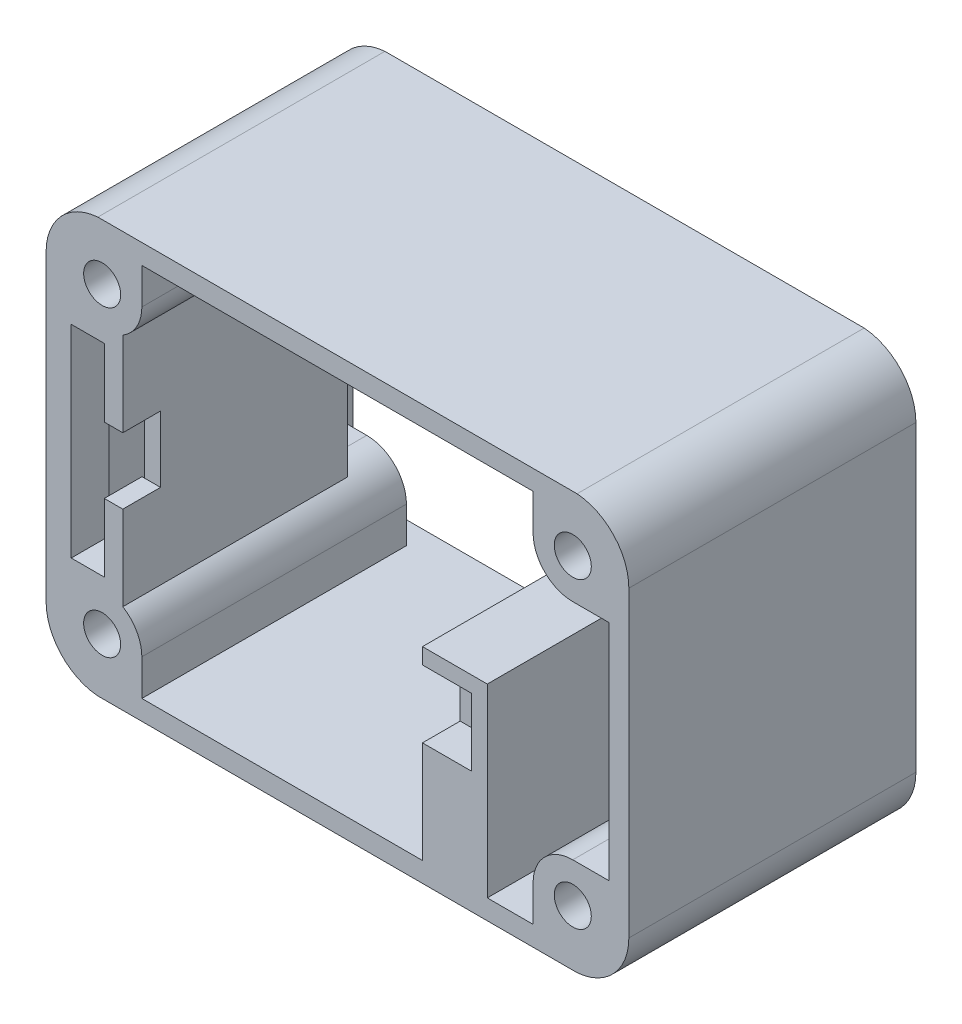
SolidWorks part; units mm, degrees
ref_plane "Front Plane" through (0, 0, 0) normal (0, 0, 1) x (1, 0, 0)
ref_plane "Top Plane" through (0, 0, 0) normal (0, 1, 0) x (1, 0, 0)
ref_plane "Right Plane" through (0, 0, 0) normal (1, 0, 0) x (0, 0, -1)
sketch "Sketch1" plane through (0, 0, 0) normal (0, 0, 1) x (1, 0, 0)
  line L0 (-20.325, 13.975) -> (-20.325, 14.175) construction
  line L1 (-22.025, -15.675) -> (22.025, -15.675)
  line L2 (-22.025, -15.675) -> (-22.025, 15.675)
  line L3 (-22.025, 15.675) -> (22.025, 15.675)
  line L4 (20.325, -13.975) -> (20.325, 13.975)
  line L5 (20.325, 13.975) -> (-20.325, 13.975)
  line L6 (-20.325, 13.975) -> (-20.325, -13.975)
  line L7 (-20.325, -13.975) -> (20.325, -13.975)
  line L8 (20.325, -13.975) -> (20.325, 13.975)
  line L9 (20.325, 13.975) -> (-20.325, 13.975)
  line L10 (-20.325, 13.975) -> (-20.325, -13.975)
  line L11 (-20.325, -13.975) -> (20.325, -13.975)
  line L12 (22.025, -15.675) -> (22.025, 15.675)
  line L13 (-22.025, -15.675) -> (22.025, 15.675) construction
  line L14 (-22.025, 15.675) -> (22.025, -15.675) construction
  line L15 (-20.325, 13.975) -> (-20.525, 13.975) construction
  line L16 (-14.7875, 11.45) -> (-14.7875, 14.175)
  line L17 (-17.7875, 8.45) -> (-20.525, 8.45)
  line L18 (0, 15.675) -> (0, -15.675) construction
  line L19 (-22.025, 0) -> (22.025, 0) construction
  line L20 (14.7875, 11.45) -> (14.7875, 14.175)
  line L21 (17.7875, 8.45) -> (20.525, 8.45)
  line L22 (17.7875, -8.45) -> (20.525, -8.45)
  line L23 (14.7875, -11.45) -> (14.7875, -14.175)
  line L24 (-14.7875, -11.45) -> (-14.7875, -14.175)
  line L25 (-17.7875, -8.45) -> (-20.525, -8.45)
  line L26 (-20.525, 14.175) -> (-22.025, 14.175) construction
  line L27 (20.525, -14.175) -> (-20.525, -14.175)
  line L28 (20.525, -14.175) -> (20.525, 14.175)
  line L29 (20.525, 14.175) -> (-20.525, 14.175)
  line L30 (-20.525, -14.175) -> (-20.525, 14.175)
  line L31 (20.525, -14.175) -> (-20.525, 14.175) construction
  line L32 (20.525, 14.175) -> (-20.525, -14.175) construction
  line L33 (-20.525, 14.175) -> (-20.525, 15.675) construction
  circle A0 centre (-17.7875, 11.45) radius 1.4
  circle A1 centre (17.7875, 11.45) radius 3
  circle A2 centre (17.7875, -11.45) radius 3
  circle A3 centre (-17.7875, -11.45) radius 3
  circle A4 centre (-17.7875, 11.45) radius 3
  circle A5 centre (17.7875, 11.45) radius 1.4
  circle A6 centre (17.7875, -11.45) radius 1.4
  circle A7 centre (-17.7875, -11.45) radius 1.4
  point P9 (0, 0)
  point P16 (0, 0)
  point P44 (-19.0562, -8.45)
  dimension "D2" = 2.8
  dimension "D4" = 6
  dimension "D3" = 1.5
  dimension "D5" = 0.2
  dimension "D1" = 0
extrude "Boss-Extrude1" add sketch "Sketch1" along normal blind 20 contours A4 L16 L9 | A4 L9 L16 L29 | L1 L12 L3 L2 A4 L29 A1 L28 A2 L27 A3 L30 | L29 A4 | A4 L29 L30 L10 L9 | A4 L9 L10 | L9 A4 L29 | L30 A4 | L10 A4 L30 | L9 A4 L10 A0 | A4 L30 L17 L10 | A4 L10 L17 | A1 L29 | L29 A1 L9 L8 L28 | L9 A1 L8 | A1 L8 L9 A5 | A1 L9 L29 | A1 L28 L8 | A1 L28 | L8 A1 L21 | L28 A1 L8 L21 | L20 A1 L9 | L9 A1 L29 L20 | A2 L28 L22 L8 | A2 L8 L22 | L8 A2 L11 A6 | L28 A2 | L28 A2 L8 | A2 L27 L28 L8 L11 | A2 L11 L8 | L11 A2 L27 | L27 A2 | A2 L23 L11 | A2 L11 L23 L27 | L27 A3 L11 L10 L30 | L11 A3 L10 | A3 L10 L30 | A3 L30 | L30 A3 L10 L25 | L10 A3 L25 | A3 L11 L10 A7 | A3 L11 L27 | A3 L27 | L24 A3 L11 | L11 A3 L27 L24
sketch "Sketch2" plane through (0, 0, 0) normal (0, 0, -1) x (-1, 0, 0)
  line L0 (-14.7875, 14.175) -> (14.7875, 14.175) construction
  line L2 (-20.525, 14.175) -> (20.525, 14.175)
  line L3 (-20.525, 14.175) -> (-20.525, -14.175)
  line L4 (-20.525, -14.175) -> (20.525, -14.175)
  line L5 (-22.025, -15.675) -> (22.025, -15.675)
  line L6 (22.025, -15.675) -> (22.025, 15.675)
  line L7 (22.025, 15.675) -> (-22.025, 15.675)
  line L8 (-22.025, 15.675) -> (-22.025, -15.675)
  line L9 (-22.025, -15.675) -> (22.025, -15.675)
  line L10 (22.025, -15.675) -> (22.025, 15.675)
  line L11 (22.025, 15.675) -> (-22.025, 15.675)
  line L12 (-22.025, 15.675) -> (-22.025, -15.675)
  line L13 (20.525, 14.175) -> (20.525, -14.175)
  line L14 (-20.525, -8.45) -> (-20.525, 8.45) construction
  line L15 (20.525, -8.45) -> (20.525, 8.45) construction
  line L16 (-14.7875, -14.175) -> (14.7875, -14.175) construction
  line L17 (0, 14.175) -> (0, -14.175) construction
  line L18 (-20.525, 0) -> (20.525, 0) construction
  line L19 (2, -14.925) -> (2, -14.175)
  line L20 (-2, 14.925) -> (2, 14.925)
  line L21 (-2, 14.925) -> (-2, 14.175)
  line L22 (-2, 14.175) -> (2, 14.175)
  line L23 (2, 14.925) -> (2, 14.175)
  line L24 (-2, 14.925) -> (2, 14.175) construction
  line L25 (-2, 14.175) -> (2, 14.925) construction
  line L26 (-21.275, -2) -> (-20.525, -2)
  line L27 (-21.275, -2) -> (-21.275, 2)
  line L28 (-21.275, 2) -> (-20.525, 2)
  line L29 (-20.525, -2) -> (-20.525, 2)
  line L30 (-21.275, -2) -> (-20.525, 2) construction
  line L31 (-21.275, 2) -> (-20.525, -2) construction
  line L32 (-2, -14.925) -> (2, -14.925)
  line L33 (-2, -14.925) -> (-2, -14.175)
  line L34 (21.275, 2) -> (20.525, 2)
  line L35 (21.275, -2) -> (21.275, 2)
  line L36 (21.275, -2) -> (20.525, -2)
  point P20 (0, 14.55)
  point P25 (-20.9, 0)
  line M25 (-22.025, -15.675) -> (22.025, -15.675)
  line M26 (22.025, -15.675) -> (22.025, 15.675)
  line M27 (22.025, 15.675) -> (-22.025, 15.675)
  line M28 (-22.025, 15.675) -> (-22.025, -15.675)
  line M36 (20.525, 8.45) -> (20.525, -8.45)
  line M41 (-14.7875, 14.175) -> (14.7875, 14.175)
  line M62 (14.7875, -14.175) -> (-14.7875, -14.175)
  line M63 (-20.525, -8.45) -> (-20.525, 8.45)
  dimension "D2" = 0.75
  dimension "D3" = 4
  dimension "D1" = 0
extrude "Boss-Extrude2" add sketch "Sketch2" along normal blind 1.7 contours L35 L36 L13 L4 L19 L32 L33 L3 L26 L27 L28 L2 L21 L20 L23 L34 M28 M25 M26 M27 M36 M62 M63 M41
ref_plane "Plane1" through (0, 0, 3) normal (0, 0, -1) x (-1, 0, 0)
sketch "Sketch3" plane through (0, 0, 3) normal (0, 0, -1) x (-1, 0, 0)
  line L0 (-20.525, 0) -> (20.525, 0) construction
  line L1 (-20.525, -2) -> (-20.525, 2) construction
  line L2 (20.525, -2) -> (20.525, 2) construction
  line L4 (-20.525, -8.45) -> (-20.525, 8.45) construction
  line L33 (20.525, 14.175) -> (20.525, 2) construction
  line L34 (16.225, -8.45) -> (20.525, -8.45)
  line L35 (16.225, -8.45) -> (16.225, 8.45)
  line L36 (16.225, 8.45) -> (20.525, 8.45)
  line L37 (20.525, -8.45) -> (20.525, 8.45)
  line L38 (16.225, -8.45) -> (20.525, 8.45) construction
  line L39 (16.225, 8.45) -> (20.525, -8.45) construction
  line L40 (17.7875, 8.45) -> (20.525, 8.45) construction
  line L41 (16.225, 8.45) -> (16.225, 8.889)
  line L42 (16.225, -8.45) -> (16.225, -8.889)
  line L43 (-8.875, 14.175) -> (-8.875, -14.175) construction
  line L44 (20.325, -7.85) -> (17.425, -7.85)
  line L45 (20.325, -7.85) -> (20.325, 7.85)
  line L46 (20.325, 7.85) -> (17.425, 7.85)
  line L47 (17.425, -7.85) -> (17.425, 7.85)
  line L48 (20.325, -7.85) -> (17.425, 7.85) construction
  line L49 (20.325, 7.85) -> (17.425, -7.85) construction
  line L50 (-20.525, 14.175) -> (-2, 14.175) construction
  line L51 (-2, -14.175) -> (-20.525, -14.175) construction
  line L52 (-10.325, -1.175) -> (-10.325, -0.175) construction
  line L53 (-6.425, -0.175) -> (-11.325, -0.175)
  line L54 (-6.425, -0.175) -> (-6.425, -14.175)
  line L55 (-6.425, -14.175) -> (-11.325, -14.175)
  line L56 (-11.325, -0.175) -> (-11.325, -14.175)
  line L57 (-6.425, -0.175) -> (-11.325, -14.175) construction
  line L58 (-6.425, -14.175) -> (-11.325, -0.175) construction
  line L59 (-10.325, -1.175) -> (-7.425, -1.175)
  line L60 (-10.325, -1.175) -> (-10.325, -6.675)
  line L61 (-10.325, -6.675) -> (-7.425, -6.675)
  line L62 (-7.425, -1.175) -> (-7.425, -6.675)
  line L63 (-10.325, -1.175) -> (-7.425, -6.675) construction
  line L64 (-10.325, -6.675) -> (-7.425, -1.175) construction
  line L65 (-10.325, -1.175) -> (-11.325, -1.175) construction
  arc A0 (-17.7875, 8.45) -> (-14.7875, 11.45) centre (-17.7875, 11.45) ccw construction
  arc A1 (-14.7875, -11.45) -> (-17.7875, -8.45) centre (-17.7875, -11.45) ccw construction
  arc A2 (-17.7875, 8.45) -> (-14.7875, 11.45) centre (-17.7875, 11.45) ccw
  arc A3 (-14.7875, -11.45) -> (-17.7875, -8.45) centre (-17.7875, -11.45) ccw
  arc A4 (14.7875, 11.45) -> (17.7875, 8.45) centre (17.7875, 11.45) ccw construction
  arc A5 (17.7875, -8.45) -> (14.7875, -11.45) centre (17.7875, -11.45) ccw construction
  arc A6 (17.7875, -8.45) -> (14.7875, -11.45) centre (17.7875, -11.45) ccw
  arc A7 (14.7875, 11.45) -> (17.7875, 8.45) centre (17.7875, 11.45) ccw
  point P41 (18.375, 0)
  point P58 (18.875, 0)
  point P71 (-8.875, -7.175)
  point P76 (-8.875, -3.925)
  dimension "D2" = 0.2
  dimension "D3" = 10.2
  dimension "D4" = 7.5
  dimension "D6" = 4.3
  dimension "D7" = 15.7
  dimension "D8" = 2.9
  dimension "D9" = 1
  dimension "D10" = 5.5
extrude "Boss-Extrude3" add sketch "Sketch3" against normal blind 14.15
sketch "Sketch4" plane through (0, 0, 17.15) normal (0, 0, 1) x (1, 0, 0)
  line L18 (11.325, -0.175) -> (6.425, -0.175)
  line L20 (-20.525, -8.45) -> (-17.7875, -8.45)
  line L21 (-16.225, -8.889) -> (-16.225, 8.889)
  line L22 (-17.7875, 8.45) -> (-20.525, 8.45)
  line L23 (-20.525, 8.45) -> (-20.525, -8.45)
  line L24 (-20.525, -8.45) -> (-17.7875, -8.45)
  line L25 (-16.225, -8.889) -> (-16.225, 8.889)
  line L26 (-17.7875, 8.45) -> (-20.525, 8.45)
  line L27 (-20.525, 8.45) -> (-20.525, -8.45)
  line L33 (-20.125, -7.65) -> (-17.625, -7.65)
  line L34 (-20.125, 7.65) -> (-20.125, -7.65)
  line L35 (11.325, -14.175) -> (11.325, -0.175)
  line L36 (6.425, -14.175) -> (11.325, -14.175)
  line L37 (6.425, -0.175) -> (6.425, -14.175)
  line L38 (11.325, -0.175) -> (6.425, -0.175)
  line L39 (11.325, -14.175) -> (11.325, -0.175)
  line L40 (6.425, -14.175) -> (11.325, -14.175)
  line L41 (6.425, -0.175) -> (6.425, -14.175)
  line L42 (-17.625, 7.65) -> (-20.125, 7.65)
  line L43 (-17.625, -7.65) -> (-17.625, 7.65)
  line L44 (-20.125, -7.65) -> (-17.625, -7.65)
  line L45 (-20.125, 7.65) -> (-20.125, -7.65)
  line L46 (7.625, -6.475) -> (10.125, -6.475)
  line L47 (7.625, -1.375) -> (7.625, -6.475)
  line L48 (10.125, -6.475) -> (10.125, -1.375)
  line L49 (10.125, -1.375) -> (7.625, -1.375)
  line L50 (7.625, -6.475) -> (10.125, -6.475)
  line L51 (7.625, -1.375) -> (7.625, -6.475)
  line L52 (10.125, -6.475) -> (10.125, -1.375)
  line L53 (10.125, -1.375) -> (7.625, -1.375)
  line L54 (-17.625, 7.65) -> (-20.125, 7.65)
  line L55 (-17.625, -7.65) -> (-17.625, 7.65)
  arc A2 (-16.225, -8.889) -> (-17.7875, -8.45) centre (-17.7875, -11.45) ccw
  arc A3 (-17.7875, 8.45) -> (-16.225, 8.889) centre (-17.7875, 11.45) ccw
  arc A4 (-16.225, -8.889) -> (-17.7875, -8.45) centre (-17.7875, -11.45) ccw
  arc A5 (-17.7875, 8.45) -> (-16.225, 8.889) centre (-17.7875, 11.45) ccw
  dimension "D1" = 0
  dimension "D2" = 0.2
  dimension "D3" = 0
  dimension "D4" = 0.2
extrude "Boss-Extrude4" add sketch "Sketch4" along normal up to surface (2.85 mm away)
sketch "Sketch5" plane through (0, 0, 20) normal (0, 0, 1) x (1, 0, 0)
  line L0 (-16.225, 0) -> (-22.025, 0) construction
  line L1 (-16.225, -8.889) -> (-16.225, 8.889) construction
  line L2 (-22.025, -15.675) -> (-22.025, 15.675) construction
  line L3 (7.625, -3.925) -> (6.425, -3.925) construction
  line L4 (7.625, -1.375) -> (7.625, -6.475) construction
  line L5 (6.425, -0.175) -> (6.425, -14.175) construction
  line L6 (-17.625, -7.65) -> (-17.625, 7.65) construction
  line L7 (-17.625, -2.5) -> (-16.225, -2.5)
  line L8 (-17.625, -2.5) -> (-17.625, 2.5)
  line L9 (-17.625, 2.5) -> (-16.225, 2.5)
  line L10 (-16.225, -2.5) -> (-16.225, 2.5)
  line L11 (-17.625, -2.5) -> (-16.225, 2.5) construction
  line L12 (-17.625, 2.5) -> (-16.225, -2.5) construction
  line L14 (6.425, -6.475) -> (7.625, -6.475)
  line L15 (6.425, -6.475) -> (6.425, -1.375)
  line L16 (6.425, -1.375) -> (7.625, -1.375)
  line L17 (7.625, -6.475) -> (7.625, -1.375)
  line L18 (6.425, -6.475) -> (7.625, -1.375) construction
  line L19 (6.425, -1.375) -> (7.625, -6.475) construction
  point P12 (-16.925, 0)
  point P19 (7.025, -3.925)
  dimension "D1" = 5
extrude "Cut-Extrude1" cut sketch "Sketch5" against normal up to surface (2.85 mm away) up to face at (8.875, -3.925, 17.15)
sketch "Sketch6" plane through (0, 0, -1.7) normal (0, 0, -1) x (-1, 0, 0)
  line L5 (-22.025, 15.675) -> (-22.025, -15.675)
  line L6 (-22.025, -15.675) -> (22.025, -15.675)
  line L7 (22.025, -15.675) -> (22.025, 15.675)
  line L8 (22.025, 15.675) -> (-22.025, 15.675)
  line L9 (-22.025, 15.675) -> (-22.025, -15.675)
  line L10 (-22.025, -15.675) -> (22.025, -15.675)
  line L11 (22.025, -15.675) -> (22.025, 15.675)
  line L12 (22.025, 15.675) -> (-22.025, 15.675)
  circle A0 centre (-17.7875, 11.45) radius 4.2375
  circle A1 centre (17.7875, 11.45) radius 4.2375
  circle A2 centre (17.7875, -11.45) radius 4.2375
  circle A3 centre (-17.7875, -11.45) radius 4.2375
  line M5 (-22.025, 15.675) -> (-22.025, -15.675)
  line M6 (-22.025, -15.675) -> (22.025, -15.675)
  line M7 (22.025, -15.675) -> (22.025, 15.675)
  line M8 (22.025, 15.675) -> (-22.025, 15.675)
  dimension "D1" = 0
extrude "Cut-Extrude2" cut sketch "Sketch6" against normal up to next contours A0 M8 M5 | A1 L11 M8 | A2 M6 M7 | A3 M5 M6
